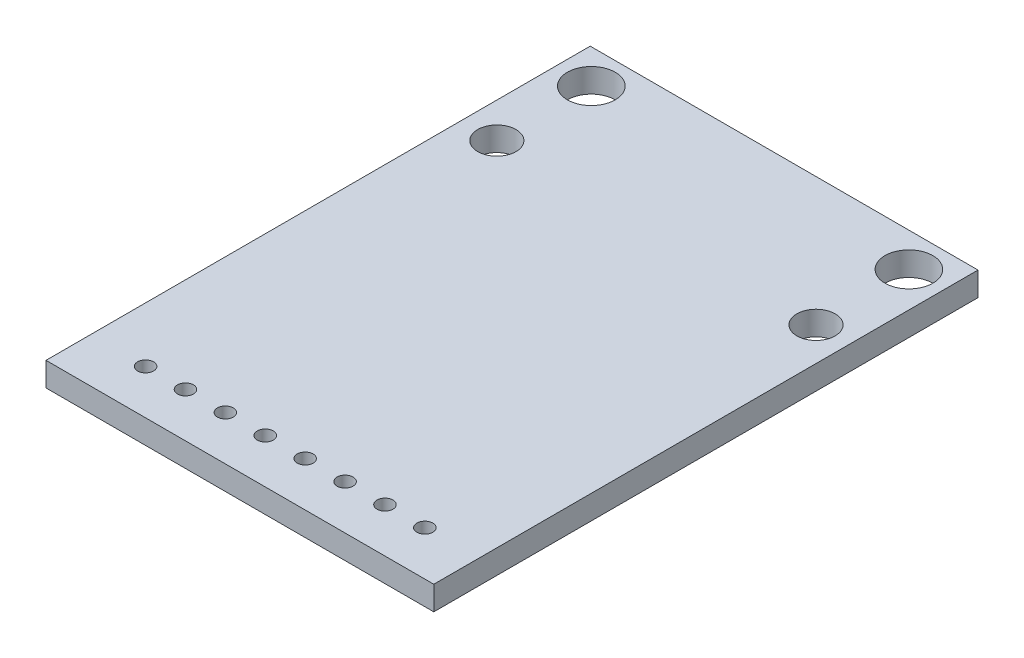
SolidWorks part; units mm, degrees
material "電力回路基板"
ref_plane "正面" through (0, 0, 0) normal (0, 0, 1) x (1, 0, 0)
ref_plane "平面" through (0, 0, 0) normal (0, 1, 0) x (1, 0, 0)
ref_plane "右側面" through (0, 0, 0) normal (1, 0, 0) x (0, 0, -1)
sketch "Sketch1" plane through (0, 0, 0) normal (0, 1, 0) x (1, 0, 0)
  line L1 (-12.15, 17.05) -> (12.15, 17.05)
  line L2 (-12.15, 17.05) -> (-12.15, -17.05)
  line L3 (-12.15, -17.05) -> (12.15, -17.05)
  line L4 (12.15, 17.05) -> (12.15, -17.05)
  line L5 (-12.15, 17.05) -> (12.15, -17.05) construction
  line L6 (-12.15, -17.05) -> (12.15, 17.05) construction
  point P0 (0, 0)
  dimension "D1" = 24.3
  dimension "D2" = 34.1
extrude "Boss-Extrude1" add sketch "Sketch1" along normal blind 1.5
sketch "Sketch2" plane through (0, 1.5, 0) normal (0, 1, 0) x (1, 0, 0)
  line L0 (0.05, 9.05) -> (-9.95, 9.05)
  line L1 (-12.15, 17.05) -> (-9.95, 17.05)
  line L2 (-12.15, 17.05) -> (-12.15, 14.92)
  line L3 (-12.15, 14.92) -> (-9.95, 14.92)
  line L4 (-9.95, 17.05) -> (-9.95, 14.92)
  line L5 (12.15, 17.05) -> (9.95, 17.05)
  line L6 (12.15, 17.05) -> (12.15, 14.92)
  line L7 (12.15, 14.92) -> (9.95, 14.92)
  line L8 (9.95, 17.05) -> (9.95, 14.92)
  line L9 (-12.15, 17.05) -> (0.05, 17.05)
  line L11 (0.05, 9.05) -> (10.05, 9.05)
  line L12 (0.05, 17.05) -> (0.05, 9.05)
  dimension "D1" = 2.2
  dimension "D2" = 2.2
  dimension "D3" = 2.13
  dimension "D4" = 2.13
  dimension "D5" = 12.2
  dimension "D6" = 8
  dimension "D7" = 10
  dimension "D8" = 10
hole_wizard "Ø3.0mm Dowel Hole1" positions "Sketch4" profile "Sketch5" hole size "Ø3.0" standard "JIS" end condition through all
sketch "Sketch4" plane through (0, 1.5, 0) normal (0, 1, 0) x (1, 0, 0)
  point P0 (-9.95, 14.92)
  point P3 (9.95, 14.92)
sketch "Sketch5" plane through (-9.95, 1.5, -14.92) normal (1, 0, 0) x (0, 0, 1)
  line L0 (0, 0) -> (0, 1.5)
  line L1 (0, 1.5) -> (1.5, 1.5)
  line L2 (1.5, 1.5) -> (1.5, 0)
  line L5 (1.5, 0) -> (0, 0)
  line L11 (0, -6.35) -> (0, 107.95) construction
  dimension "Thru Hole Dia." = 3
  dimension "Thru Hole Depth" = 1.5
hole_wizard "M2 Clearance Hole1" positions "Sketch7" profile "Sketch8" hole size "M2" standard "JIS" end condition through all
sketch "Sketch7" plane through (0, 1.5, 0) normal (0, 1, 0) x (1, 0, 0)
  line L0 (12.15, 17.05) -> (-12.15, 17.05) construction
  point P8 (-9.95, 9)
  point P10 (10.05, 9)
  point P15 (0, 0)
  point P16 (0, 0)
  dimension "D1" = 8.05
  dimension "D2" = 8.05
sketch "Sketch8" plane through (-9.95, 1.5, -9) normal (1, 0, 0) x (0, 0, 1)
  line L0 (0, 0) -> (0, 1.5)
  line L1 (0, 1.5) -> (1.2, 1.5)
  line L2 (1.2, 1.5) -> (1.2, 0)
  line L5 (1.2, 0) -> (0, 0)
  line L11 (0, -6.35) -> (0, 107.95) construction
  dimension "Thru Hole Dia." = 2.4
  dimension "Thru Hole Depth" = 1.5
sketch "Sketch9" plane through (0, 1.5, 0) normal (0, 1, 0) x (1, 0, 0)
  line L0 (-12.15, 17.05) -> (-12.15, -17.05) construction
  line L1 (-12.15, -17.05) -> (12.15, -17.05) construction
  circle A0 centre (-8.7, -14.26) radius 0.5
  circle A1 centre (-6.2, -14.26) radius 0.5
  circle A2 centre (-3.7, -14.26) radius 0.5
  circle A3 centre (-1.2, -14.26) radius 0.5
  circle A4 centre (1.3, -14.26) radius 0.5
  circle A5 centre (3.8, -14.26) radius 0.5
  circle A6 centre (6.3, -14.26) radius 0.5
  circle A7 centre (8.8, -14.26) radius 0.5
  dimension "D1" = 3.45
  dimension "D2" = 2.79
  dimension "D3" = 8
extrude "Cut-Extrude1" cut sketch "Sketch9" against normal up to next
